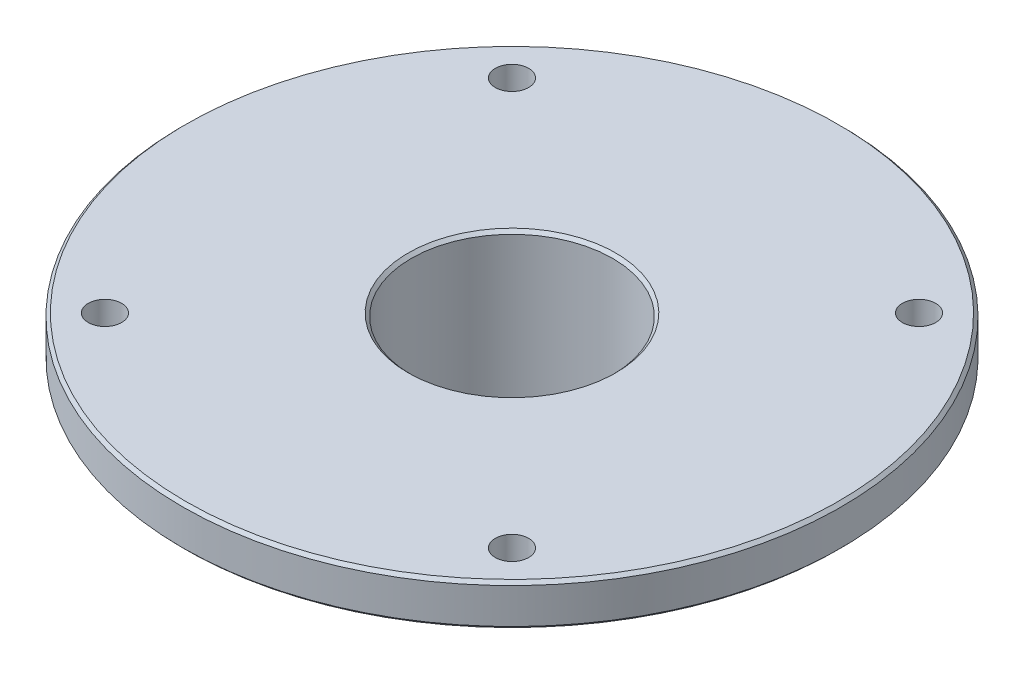
SolidWorks part; units mm, degrees
material "AISI 1045 Steel, cold drawn"
ref_plane "Front Plane" through (0, 0, 0) normal (0, 0, 1) x (1, 0, 0)
ref_plane "Top Plane" through (0, 0, 0) normal (0, 1, 0) x (1, 0, 0)
ref_plane "Right Plane" through (0, 0, 0) normal (1, 0, 0) x (0, 0, -1)
sketch "Sketch1" plane through (0, 0, 0) normal (0, 0, 1) x (1, 0, 0)
  line L0 (-24.15, 5.5193) -> (-24.15, -34.4807)
  line L1 (-24.15, -34.4807) -> (-30, -34.4807)
  line L2 (-30, -34.4807) -> (-30, -6.4807)
  line L3 (-30, -6.4807) -> (-36, -6.4807)
  line L4 (-36, -6.4807) -> (-36, -4.4807)
  line L5 (-36, -4.4807) -> (-79, -4.4807)
  line L6 (-79, -4.4807) -> (-79, 5.5193)
  line L7 (-79, 5.5193) -> (-24.15, 5.5193)
  line L8 (0, 0) -> (0, -23.4267) construction
  dimension "D1" = 79
  dimension "D2" = 2
  dimension "D3" = 36
  dimension "D4" = 24.15
  dimension "D5" = 30
  dimension "D6" = 28
  dimension "D7" = 10
  dimension "D8" = 40
revolve "Revolve1" add sketch "Sketch1" angle 360 about L8
sketch "Sketch2" plane through (0, 5.5193, 0) normal (0, 1, 0) x (1, 0, 0)
  line L1 (-48.7904, -48.7904) -> (48.7904, -48.7904) construction
  line L2 (-48.7904, -48.7904) -> (-48.7904, 48.7904) construction
  line L3 (-48.7904, 48.7904) -> (48.7904, 48.7904) construction
  line L4 (48.7904, -48.7904) -> (48.7904, 48.7904) construction
  line L5 (-48.7904, -48.7904) -> (48.7904, 48.7904) construction
  line L6 (-48.7904, 48.7904) -> (48.7904, -48.7904) construction
  circle A0 centre (48.7904, 48.7904) radius 4
  circle A1 centre (48.7904, -48.7904) radius 4
  circle A2 centre (-48.7904, -48.7904) radius 4
  circle A3 centre (-48.7904, 48.7904) radius 4
  point P0 (0, 0)
  dimension "D2" = 8
  dimension "D1" = 138
extrude "Cut-Extrude1" cut sketch "Sketch2" against normal up to next
chamfer "Chamfer1" distance 0.75 angle 45 5 edges at (0, -34.4807, 30) (0, -4.4807, 79) (0, 5.5193, 79) (0, -34.4807, 24.15) (0, 5.5193, 24.15)
